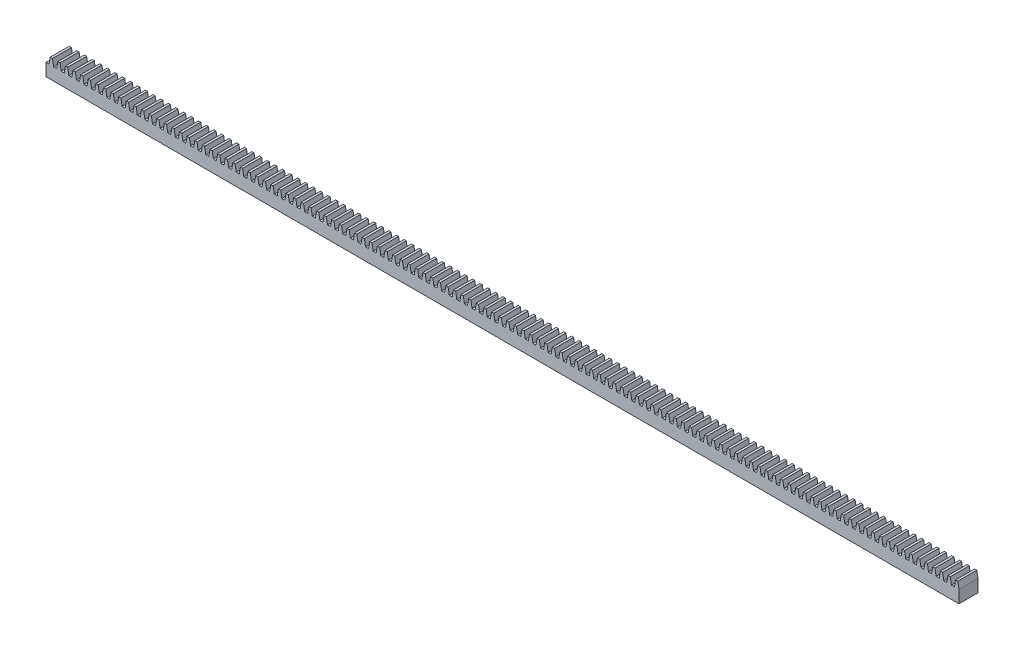
SolidWorks part; units mm, degrees
ref_plane "Front Plane" through (0, 0, 0) normal (0, 0, 1) x (1, 0, 0)
ref_plane "Top Plane" through (0, 0, 0) normal (0, 1, 0) x (1, 0, 0)
ref_plane "Right Plane" through (0, 0, 0) normal (1, 0, 0) x (0, 0, -1)
sketch "Sketch1" plane through (0, 0, 0) normal (1, 0, 0) x (0, 0, -1)
  line L1 (0, 0) -> (6.35, 0)
  line L2 (0, 0) -> (0, 6.35)
  line L3 (0, 6.35) -> (6.35, 6.35)
  line L4 (6.35, 0) -> (6.35, 6.35)
  dimension "D1" = 6.35
  dimension "D2" = 6.35
extrude "Boss-Extrude1" add sketch "Sketch1" against normal blind 304.8
sketch "Sketch2" plane through (0, 0, 0) normal (0, 0, 1) x (1, 0, 0)
  line L0 (0, 6.35) -> (0, 0) construction
  line L1 (-5.08, 4.1402) -> (-5.4696, 6.35)
  line L2 (-4.064, 4.1402) -> (-5.08, 4.1402)
  line L3 (-4.064, 4.1402) -> (-3.6744, 6.35)
  line L4 (-5.4696, 6.35) -> (-3.6744, 6.35)
  line L5 (-1.524, 4.1402) -> (-1.1344, 6.35)
  line L6 (-2.54, 4.1402) -> (-2.9296, 6.35)
  line L7 (-2.9296, 6.35) -> (-1.1344, 6.35)
  line L8 (-7.62, 4.1402) -> (-8.0096, 6.35)
  line L9 (-1.524, 4.1402) -> (-2.54, 4.1402)
  line L10 (-6.604, 4.1402) -> (-7.62, 4.1402)
  line L11 (-6.604, 4.1402) -> (-6.2144, 6.35)
  line L12 (-8.0096, 6.35) -> (-6.2144, 6.35)
  line L13 (-10.16, 4.1402) -> (-10.5496, 6.35)
  line L14 (-9.144, 4.1402) -> (-10.16, 4.1402)
  line L15 (-9.144, 4.1402) -> (-8.7544, 6.35)
  line L16 (-10.5496, 6.35) -> (-8.7544, 6.35)
  line L17 (-12.7, 4.1402) -> (-13.0896, 6.35)
  line L18 (-11.684, 4.1402) -> (-12.7, 4.1402)
  line L19 (-11.684, 4.1402) -> (-11.2944, 6.35)
  line L20 (-13.0896, 6.35) -> (-11.2944, 6.35)
  line L21 (-15.24, 4.1402) -> (-15.6296, 6.35)
  line L22 (-14.224, 4.1402) -> (-15.24, 4.1402)
  line L23 (-14.224, 4.1402) -> (-13.8344, 6.35)
  line L24 (-15.6296, 6.35) -> (-13.8344, 6.35)
  line L25 (-17.78, 4.1402) -> (-18.1696, 6.35)
  line L26 (-16.764, 4.1402) -> (-17.78, 4.1402)
  line L27 (-16.764, 4.1402) -> (-16.3744, 6.35)
  line L28 (-18.1696, 6.35) -> (-16.3744, 6.35)
  line L29 (-20.32, 4.1402) -> (-20.7096, 6.35)
  line L30 (-19.304, 4.1402) -> (-20.32, 4.1402)
  line L31 (-19.304, 4.1402) -> (-18.9144, 6.35)
  line L32 (-20.7096, 6.35) -> (-18.9144, 6.35)
  line L33 (-22.86, 4.1402) -> (-23.2496, 6.35)
  line L34 (-21.844, 4.1402) -> (-22.86, 4.1402)
  line L35 (-21.844, 4.1402) -> (-21.4544, 6.35)
  line L36 (-23.2496, 6.35) -> (-21.4544, 6.35)
  line L37 (-25.4, 4.1402) -> (-25.7896, 6.35)
  line L38 (-24.384, 4.1402) -> (-25.4, 4.1402)
  line L39 (-24.384, 4.1402) -> (-23.9944, 6.35)
  line L40 (-25.7896, 6.35) -> (-23.9944, 6.35)
  line L41 (-27.94, 4.1402) -> (-28.3296, 6.35)
  line L42 (-26.924, 4.1402) -> (-27.94, 4.1402)
  line L43 (-26.924, 4.1402) -> (-26.5344, 6.35)
  line L44 (-28.3296, 6.35) -> (-26.5344, 6.35)
  line L45 (-30.48, 4.1402) -> (-30.8696, 6.35)
  line L46 (-29.464, 4.1402) -> (-30.48, 4.1402)
  line L47 (-29.464, 4.1402) -> (-29.0744, 6.35)
  line L48 (-30.8696, 6.35) -> (-29.0744, 6.35)
  line L49 (-33.02, 4.1402) -> (-33.4096, 6.35)
  line L50 (-32.004, 4.1402) -> (-33.02, 4.1402)
  line L51 (-32.004, 4.1402) -> (-31.6144, 6.35)
  line L52 (-33.4096, 6.35) -> (-31.6144, 6.35)
  line L53 (-35.56, 4.1402) -> (-35.9496, 6.35)
  line L54 (-34.544, 4.1402) -> (-35.56, 4.1402)
  line L55 (-34.544, 4.1402) -> (-34.1544, 6.35)
  line L56 (-35.9496, 6.35) -> (-34.1544, 6.35)
  line L57 (-38.1, 4.1402) -> (-38.4896, 6.35)
  line L58 (-37.084, 4.1402) -> (-38.1, 4.1402)
  line L59 (-37.084, 4.1402) -> (-36.6944, 6.35)
  line L60 (-38.4896, 6.35) -> (-36.6944, 6.35)
  line L61 (-40.64, 4.1402) -> (-41.0296, 6.35)
  line L62 (-39.624, 4.1402) -> (-40.64, 4.1402)
  line L63 (-39.624, 4.1402) -> (-39.2344, 6.35)
  line L64 (-41.0296, 6.35) -> (-39.2344, 6.35)
  line L65 (-43.18, 4.1402) -> (-43.5696, 6.35)
  line L66 (-42.164, 4.1402) -> (-43.18, 4.1402)
  line L67 (-42.164, 4.1402) -> (-41.7744, 6.35)
  line L68 (-43.5696, 6.35) -> (-41.7744, 6.35)
  line L69 (-45.72, 4.1402) -> (-46.1096, 6.35)
  line L70 (-44.704, 4.1402) -> (-45.72, 4.1402)
  line L71 (-44.704, 4.1402) -> (-44.3144, 6.35)
  line L72 (-46.1096, 6.35) -> (-44.3144, 6.35)
  line L73 (-48.26, 4.1402) -> (-48.6496, 6.35)
  line L74 (-47.244, 4.1402) -> (-48.26, 4.1402)
  line L75 (-47.244, 4.1402) -> (-46.8544, 6.35)
  line L76 (-48.6496, 6.35) -> (-46.8544, 6.35)
  line L77 (-50.8, 4.1402) -> (-51.1896, 6.35)
  line L78 (-49.784, 4.1402) -> (-50.8, 4.1402)
  line L79 (-49.784, 4.1402) -> (-49.3944, 6.35)
  line L80 (-51.1896, 6.35) -> (-49.3944, 6.35)
  line L81 (-53.34, 4.1402) -> (-53.7296, 6.35)
  line L82 (-52.324, 4.1402) -> (-53.34, 4.1402)
  line L83 (-52.324, 4.1402) -> (-51.9344, 6.35)
  line L84 (-53.7296, 6.35) -> (-51.9344, 6.35)
  line L85 (-55.88, 4.1402) -> (-56.2696, 6.35)
  line L86 (-54.864, 4.1402) -> (-55.88, 4.1402)
  line L87 (-54.864, 4.1402) -> (-54.4744, 6.35)
  line L88 (-56.2696, 6.35) -> (-54.4744, 6.35)
  line L89 (-58.42, 4.1402) -> (-58.8096, 6.35)
  line L90 (-57.404, 4.1402) -> (-58.42, 4.1402)
  line L91 (-57.404, 4.1402) -> (-57.0144, 6.35)
  line L92 (-58.8096, 6.35) -> (-57.0144, 6.35)
  line L93 (-60.96, 4.1402) -> (-61.3496, 6.35)
  line L94 (-59.944, 4.1402) -> (-60.96, 4.1402)
  line L95 (-59.944, 4.1402) -> (-59.5544, 6.35)
  line L96 (-61.3496, 6.35) -> (-59.5544, 6.35)
  line L97 (-63.5, 4.1402) -> (-63.8896, 6.35)
  line L98 (-62.484, 4.1402) -> (-63.5, 4.1402)
  line L99 (-62.484, 4.1402) -> (-62.0944, 6.35)
  line L100 (-63.8896, 6.35) -> (-62.0944, 6.35)
  line L101 (-66.04, 4.1402) -> (-66.4296, 6.35)
  line L102 (-65.024, 4.1402) -> (-66.04, 4.1402)
  line L103 (-65.024, 4.1402) -> (-64.6344, 6.35)
  line L104 (-66.4296, 6.35) -> (-64.6344, 6.35)
  line L105 (-68.58, 4.1402) -> (-68.9696, 6.35)
  line L106 (-67.564, 4.1402) -> (-68.58, 4.1402)
  line L107 (-67.564, 4.1402) -> (-67.1744, 6.35)
  line L108 (-68.9696, 6.35) -> (-67.1744, 6.35)
  line L109 (-71.12, 4.1402) -> (-71.5096, 6.35)
  line L110 (-70.104, 4.1402) -> (-71.12, 4.1402)
  line L111 (-70.104, 4.1402) -> (-69.7144, 6.35)
  line L112 (-71.5096, 6.35) -> (-69.7144, 6.35)
  line L113 (-73.66, 4.1402) -> (-74.0496, 6.35)
  line L114 (-72.644, 4.1402) -> (-73.66, 4.1402)
  line L115 (-72.644, 4.1402) -> (-72.2544, 6.35)
  line L116 (-74.0496, 6.35) -> (-72.2544, 6.35)
  line L117 (-76.2, 4.1402) -> (-76.5896, 6.35)
  line L118 (-75.184, 4.1402) -> (-76.2, 4.1402)
  line L119 (-75.184, 4.1402) -> (-74.7944, 6.35)
  line L120 (-76.5896, 6.35) -> (-74.7944, 6.35)
  line L121 (-78.74, 4.1402) -> (-79.1296, 6.35)
  line L122 (-77.724, 4.1402) -> (-78.74, 4.1402)
  line L123 (-77.724, 4.1402) -> (-77.3344, 6.35)
  line L124 (-79.1296, 6.35) -> (-77.3344, 6.35)
  line L125 (-81.28, 4.1402) -> (-81.6696, 6.35)
  line L126 (-80.264, 4.1402) -> (-81.28, 4.1402)
  line L127 (-80.264, 4.1402) -> (-79.8744, 6.35)
  line L128 (-81.6696, 6.35) -> (-79.8744, 6.35)
  line L129 (-83.82, 4.1402) -> (-84.2096, 6.35)
  line L130 (-82.804, 4.1402) -> (-83.82, 4.1402)
  line L131 (-82.804, 4.1402) -> (-82.4144, 6.35)
  line L132 (-84.2096, 6.35) -> (-82.4144, 6.35)
  line L133 (-86.36, 4.1402) -> (-86.7496, 6.35)
  line L134 (-85.344, 4.1402) -> (-86.36, 4.1402)
  line L135 (-85.344, 4.1402) -> (-84.9544, 6.35)
  line L136 (-86.7496, 6.35) -> (-84.9544, 6.35)
  line L137 (-88.9, 4.1402) -> (-89.2896, 6.35)
  line L138 (-87.884, 4.1402) -> (-88.9, 4.1402)
  line L139 (-87.884, 4.1402) -> (-87.4944, 6.35)
  line L140 (-89.2896, 6.35) -> (-87.4944, 6.35)
  line L141 (-91.44, 4.1402) -> (-91.8296, 6.35)
  line L142 (-90.424, 4.1402) -> (-91.44, 4.1402)
  line L143 (-90.424, 4.1402) -> (-90.0344, 6.35)
  line L144 (-91.8296, 6.35) -> (-90.0344, 6.35)
  line L145 (-93.98, 4.1402) -> (-94.3696, 6.35)
  line L146 (-92.964, 4.1402) -> (-93.98, 4.1402)
  line L147 (-92.964, 4.1402) -> (-92.5744, 6.35)
  line L148 (-94.3696, 6.35) -> (-92.5744, 6.35)
  line L149 (-96.52, 4.1402) -> (-96.9096, 6.35)
  line L150 (-95.504, 4.1402) -> (-96.52, 4.1402)
  line L151 (-95.504, 4.1402) -> (-95.1144, 6.35)
  line L152 (-96.9096, 6.35) -> (-95.1144, 6.35)
  line L153 (-99.06, 4.1402) -> (-99.4496, 6.35)
  line L154 (-98.044, 4.1402) -> (-99.06, 4.1402)
  line L155 (-98.044, 4.1402) -> (-97.6544, 6.35)
  line L156 (-99.4496, 6.35) -> (-97.6544, 6.35)
  line L157 (-101.6, 4.1402) -> (-101.9896, 6.35)
  line L158 (-100.584, 4.1402) -> (-101.6, 4.1402)
  line L159 (-100.584, 4.1402) -> (-100.1944, 6.35)
  line L160 (-101.9896, 6.35) -> (-100.1944, 6.35)
  line L161 (-104.14, 4.1402) -> (-104.5296, 6.35)
  line L162 (-103.124, 4.1402) -> (-104.14, 4.1402)
  line L163 (-103.124, 4.1402) -> (-102.7344, 6.35)
  line L164 (-104.5296, 6.35) -> (-102.7344, 6.35)
  line L165 (-106.68, 4.1402) -> (-107.0696, 6.35)
  line L166 (-105.664, 4.1402) -> (-106.68, 4.1402)
  line L167 (-105.664, 4.1402) -> (-105.2744, 6.35)
  line L168 (-107.0696, 6.35) -> (-105.2744, 6.35)
  line L169 (-109.22, 4.1402) -> (-109.6096, 6.35)
  line L170 (-108.204, 4.1402) -> (-109.22, 4.1402)
  line L171 (-108.204, 4.1402) -> (-107.8144, 6.35)
  line L172 (-109.6096, 6.35) -> (-107.8144, 6.35)
  line L173 (-111.76, 4.1402) -> (-112.1496, 6.35)
  line L174 (-110.744, 4.1402) -> (-111.76, 4.1402)
  line L175 (-110.744, 4.1402) -> (-110.3544, 6.35)
  line L176 (-112.1496, 6.35) -> (-110.3544, 6.35)
  line L177 (-114.3, 4.1402) -> (-114.6896, 6.35)
  line L178 (-113.284, 4.1402) -> (-114.3, 4.1402)
  line L179 (-113.284, 4.1402) -> (-112.8944, 6.35)
  line L180 (-114.6896, 6.35) -> (-112.8944, 6.35)
  line L181 (-116.84, 4.1402) -> (-117.2296, 6.35)
  line L182 (-115.824, 4.1402) -> (-116.84, 4.1402)
  line L183 (-115.824, 4.1402) -> (-115.4344, 6.35)
  line L184 (-117.2296, 6.35) -> (-115.4344, 6.35)
  line L185 (-119.38, 4.1402) -> (-119.7696, 6.35)
  line L186 (-118.364, 4.1402) -> (-119.38, 4.1402)
  line L187 (-118.364, 4.1402) -> (-117.9744, 6.35)
  line L188 (-119.7696, 6.35) -> (-117.9744, 6.35)
  line L189 (-121.92, 4.1402) -> (-122.3096, 6.35)
  line L190 (-120.904, 4.1402) -> (-121.92, 4.1402)
  line L191 (-120.904, 4.1402) -> (-120.5144, 6.35)
  line L192 (-122.3096, 6.35) -> (-120.5144, 6.35)
  line L193 (-124.46, 4.1402) -> (-124.8496, 6.35)
  line L194 (-123.444, 4.1402) -> (-124.46, 4.1402)
  line L195 (-123.444, 4.1402) -> (-123.0544, 6.35)
  line L196 (-124.8496, 6.35) -> (-123.0544, 6.35)
  line L197 (-127, 4.1402) -> (-127.3896, 6.35)
  line L198 (-125.984, 4.1402) -> (-127, 4.1402)
  line L199 (-125.984, 4.1402) -> (-125.5944, 6.35)
  line L200 (-127.3896, 6.35) -> (-125.5944, 6.35)
  line L201 (-129.54, 4.1402) -> (-129.9296, 6.35)
  line L202 (-128.524, 4.1402) -> (-129.54, 4.1402)
  line L203 (-128.524, 4.1402) -> (-128.1344, 6.35)
  line L204 (-129.9296, 6.35) -> (-128.1344, 6.35)
  line L205 (-132.08, 4.1402) -> (-132.4696, 6.35)
  line L206 (-131.064, 4.1402) -> (-132.08, 4.1402)
  line L207 (-131.064, 4.1402) -> (-130.6744, 6.35)
  line L208 (-132.4696, 6.35) -> (-130.6744, 6.35)
  line L209 (-134.62, 4.1402) -> (-135.0096, 6.35)
  line L210 (-133.604, 4.1402) -> (-134.62, 4.1402)
  line L211 (-133.604, 4.1402) -> (-133.2144, 6.35)
  line L212 (-135.0096, 6.35) -> (-133.2144, 6.35)
  line L213 (-137.16, 4.1402) -> (-137.5496, 6.35)
  line L214 (-136.144, 4.1402) -> (-137.16, 4.1402)
  line L215 (-136.144, 4.1402) -> (-135.7544, 6.35)
  line L216 (-137.5496, 6.35) -> (-135.7544, 6.35)
  line L217 (-139.7, 4.1402) -> (-140.0896, 6.35)
  line L218 (-138.684, 4.1402) -> (-139.7, 4.1402)
  line L219 (-138.684, 4.1402) -> (-138.2944, 6.35)
  line L220 (-140.0896, 6.35) -> (-138.2944, 6.35)
  line L221 (-142.24, 4.1402) -> (-142.6296, 6.35)
  line L222 (-141.224, 4.1402) -> (-142.24, 4.1402)
  line L223 (-141.224, 4.1402) -> (-140.8344, 6.35)
  line L224 (-142.6296, 6.35) -> (-140.8344, 6.35)
  line L225 (-144.78, 4.1402) -> (-145.1696, 6.35)
  line L226 (-143.764, 4.1402) -> (-144.78, 4.1402)
  line L227 (-143.764, 4.1402) -> (-143.3744, 6.35)
  line L228 (-145.1696, 6.35) -> (-143.3744, 6.35)
  line L229 (-147.32, 4.1402) -> (-147.7096, 6.35)
  line L230 (-146.304, 4.1402) -> (-147.32, 4.1402)
  line L231 (-146.304, 4.1402) -> (-145.9144, 6.35)
  line L232 (-147.7096, 6.35) -> (-145.9144, 6.35)
  line L233 (-149.86, 4.1402) -> (-150.2496, 6.35)
  line L234 (-148.844, 4.1402) -> (-149.86, 4.1402)
  line L235 (-148.844, 4.1402) -> (-148.4544, 6.35)
  line L236 (-150.2496, 6.35) -> (-148.4544, 6.35)
  line L237 (-152.4, 4.1402) -> (-152.7896, 6.35)
  line L238 (-151.384, 4.1402) -> (-152.4, 4.1402)
  line L239 (-151.384, 4.1402) -> (-150.9944, 6.35)
  line L240 (-152.7896, 6.35) -> (-150.9944, 6.35)
  line L241 (-154.94, 4.1402) -> (-155.3296, 6.35)
  line L242 (-153.924, 4.1402) -> (-154.94, 4.1402)
  line L243 (-153.924, 4.1402) -> (-153.5344, 6.35)
  line L244 (-155.3296, 6.35) -> (-153.5344, 6.35)
  line L245 (-157.48, 4.1402) -> (-157.8696, 6.35)
  line L246 (-156.464, 4.1402) -> (-157.48, 4.1402)
  line L247 (-156.464, 4.1402) -> (-156.0744, 6.35)
  line L248 (-157.8696, 6.35) -> (-156.0744, 6.35)
  line L249 (-160.02, 4.1402) -> (-160.4096, 6.35)
  line L250 (-159.004, 4.1402) -> (-160.02, 4.1402)
  line L251 (-159.004, 4.1402) -> (-158.6144, 6.35)
  line L252 (-160.4096, 6.35) -> (-158.6144, 6.35)
  line L253 (-162.56, 4.1402) -> (-162.9496, 6.35)
  line L254 (-161.544, 4.1402) -> (-162.56, 4.1402)
  line L255 (-161.544, 4.1402) -> (-161.1544, 6.35)
  line L256 (-162.9496, 6.35) -> (-161.1544, 6.35)
  line L257 (-165.1, 4.1402) -> (-165.4896, 6.35)
  line L258 (-164.084, 4.1402) -> (-165.1, 4.1402)
  line L259 (-164.084, 4.1402) -> (-163.6944, 6.35)
  line L260 (-165.4896, 6.35) -> (-163.6944, 6.35)
  line L261 (-167.64, 4.1402) -> (-168.0296, 6.35)
  line L262 (-166.624, 4.1402) -> (-167.64, 4.1402)
  line L263 (-166.624, 4.1402) -> (-166.2344, 6.35)
  line L264 (-168.0296, 6.35) -> (-166.2344, 6.35)
  line L265 (-170.18, 4.1402) -> (-170.5696, 6.35)
  line L266 (-169.164, 4.1402) -> (-170.18, 4.1402)
  line L267 (-169.164, 4.1402) -> (-168.7744, 6.35)
  line L268 (-170.5696, 6.35) -> (-168.7744, 6.35)
  line L269 (-172.72, 4.1402) -> (-173.1096, 6.35)
  line L270 (-171.704, 4.1402) -> (-172.72, 4.1402)
  line L271 (-171.704, 4.1402) -> (-171.3144, 6.35)
  line L272 (-173.1096, 6.35) -> (-171.3144, 6.35)
  line L273 (-175.26, 4.1402) -> (-175.6496, 6.35)
  line L274 (-174.244, 4.1402) -> (-175.26, 4.1402)
  line L275 (-174.244, 4.1402) -> (-173.8544, 6.35)
  line L276 (-175.6496, 6.35) -> (-173.8544, 6.35)
  line L277 (-177.8, 4.1402) -> (-178.1896, 6.35)
  line L278 (-176.784, 4.1402) -> (-177.8, 4.1402)
  line L279 (-176.784, 4.1402) -> (-176.3944, 6.35)
  line L280 (-178.1896, 6.35) -> (-176.3944, 6.35)
  line L281 (-180.34, 4.1402) -> (-180.7296, 6.35)
  line L282 (-179.324, 4.1402) -> (-180.34, 4.1402)
  line L283 (-179.324, 4.1402) -> (-178.9344, 6.35)
  line L284 (-180.7296, 6.35) -> (-178.9344, 6.35)
  line L285 (-182.88, 4.1402) -> (-183.2696, 6.35)
  line L286 (-181.864, 4.1402) -> (-182.88, 4.1402)
  line L287 (-181.864, 4.1402) -> (-181.4744, 6.35)
  line L288 (-183.2696, 6.35) -> (-181.4744, 6.35)
  line L289 (-185.42, 4.1402) -> (-185.8096, 6.35)
  line L290 (-184.404, 4.1402) -> (-185.42, 4.1402)
  line L291 (-184.404, 4.1402) -> (-184.0144, 6.35)
  line L292 (-185.8096, 6.35) -> (-184.0144, 6.35)
  line L293 (-187.96, 4.1402) -> (-188.3496, 6.35)
  line L294 (-186.944, 4.1402) -> (-187.96, 4.1402)
  line L295 (-186.944, 4.1402) -> (-186.5544, 6.35)
  line L296 (-188.3496, 6.35) -> (-186.5544, 6.35)
  line L297 (-190.5, 4.1402) -> (-190.8896, 6.35)
  line L298 (-189.484, 4.1402) -> (-190.5, 4.1402)
  line L299 (-189.484, 4.1402) -> (-189.0944, 6.35)
  line L300 (-190.8896, 6.35) -> (-189.0944, 6.35)
  line L301 (-193.04, 4.1402) -> (-193.4296, 6.35)
  line L302 (-192.024, 4.1402) -> (-193.04, 4.1402)
  line L303 (-192.024, 4.1402) -> (-191.6344, 6.35)
  line L304 (-193.4296, 6.35) -> (-191.6344, 6.35)
  line L305 (-195.58, 4.1402) -> (-195.9696, 6.35)
  line L306 (-194.564, 4.1402) -> (-195.58, 4.1402)
  line L307 (-194.564, 4.1402) -> (-194.1744, 6.35)
  line L308 (-195.9696, 6.35) -> (-194.1744, 6.35)
  line L309 (-198.12, 4.1402) -> (-198.5096, 6.35)
  line L310 (-197.104, 4.1402) -> (-198.12, 4.1402)
  line L311 (-197.104, 4.1402) -> (-196.7144, 6.35)
  line L312 (-198.5096, 6.35) -> (-196.7144, 6.35)
  line L313 (-200.66, 4.1402) -> (-201.0496, 6.35)
  line L314 (-199.644, 4.1402) -> (-200.66, 4.1402)
  line L315 (-199.644, 4.1402) -> (-199.2544, 6.35)
  line L316 (-201.0496, 6.35) -> (-199.2544, 6.35)
  line L317 (-203.2, 4.1402) -> (-203.5896, 6.35)
  line L318 (-202.184, 4.1402) -> (-203.2, 4.1402)
  line L319 (-202.184, 4.1402) -> (-201.7944, 6.35)
  line L320 (-203.5896, 6.35) -> (-201.7944, 6.35)
  line L321 (-205.74, 4.1402) -> (-206.1296, 6.35)
  line L322 (-204.724, 4.1402) -> (-205.74, 4.1402)
  line L323 (-204.724, 4.1402) -> (-204.3344, 6.35)
  line L324 (-206.1296, 6.35) -> (-204.3344, 6.35)
  line L325 (-208.28, 4.1402) -> (-208.6696, 6.35)
  line L326 (-207.264, 4.1402) -> (-208.28, 4.1402)
  line L327 (-207.264, 4.1402) -> (-206.8744, 6.35)
  line L328 (-208.6696, 6.35) -> (-206.8744, 6.35)
  line L329 (-210.82, 4.1402) -> (-211.2096, 6.35)
  line L330 (-209.804, 4.1402) -> (-210.82, 4.1402)
  line L331 (-209.804, 4.1402) -> (-209.4144, 6.35)
  line L332 (-211.2096, 6.35) -> (-209.4144, 6.35)
  line L333 (-213.36, 4.1402) -> (-213.7496, 6.35)
  line L334 (-212.344, 4.1402) -> (-213.36, 4.1402)
  line L335 (-212.344, 4.1402) -> (-211.9544, 6.35)
  line L336 (-213.7496, 6.35) -> (-211.9544, 6.35)
  line L337 (-215.9, 4.1402) -> (-216.2896, 6.35)
  line L338 (-214.884, 4.1402) -> (-215.9, 4.1402)
  line L339 (-214.884, 4.1402) -> (-214.4944, 6.35)
  line L340 (-216.2896, 6.35) -> (-214.4944, 6.35)
  line L341 (-218.44, 4.1402) -> (-218.8296, 6.35)
  line L342 (-217.424, 4.1402) -> (-218.44, 4.1402)
  line L343 (-217.424, 4.1402) -> (-217.0344, 6.35)
  line L344 (-218.8296, 6.35) -> (-217.0344, 6.35)
  line L345 (-220.98, 4.1402) -> (-221.3696, 6.35)
  line L346 (-219.964, 4.1402) -> (-220.98, 4.1402)
  line L347 (-219.964, 4.1402) -> (-219.5744, 6.35)
  line L348 (-221.3696, 6.35) -> (-219.5744, 6.35)
  line L349 (-223.52, 4.1402) -> (-223.9096, 6.35)
  line L350 (-222.504, 4.1402) -> (-223.52, 4.1402)
  line L351 (-222.504, 4.1402) -> (-222.1144, 6.35)
  line L352 (-223.9096, 6.35) -> (-222.1144, 6.35)
  line L353 (-226.06, 4.1402) -> (-226.4496, 6.35)
  line L354 (-225.044, 4.1402) -> (-226.06, 4.1402)
  line L355 (-225.044, 4.1402) -> (-224.6544, 6.35)
  line L356 (-226.4496, 6.35) -> (-224.6544, 6.35)
  line L357 (-228.6, 4.1402) -> (-228.9896, 6.35)
  line L358 (-227.584, 4.1402) -> (-228.6, 4.1402)
  line L359 (-227.584, 4.1402) -> (-227.1944, 6.35)
  line L360 (-228.9896, 6.35) -> (-227.1944, 6.35)
  line L361 (-231.14, 4.1402) -> (-231.5296, 6.35)
  line L362 (-230.124, 4.1402) -> (-231.14, 4.1402)
  line L363 (-230.124, 4.1402) -> (-229.7344, 6.35)
  line L364 (-231.5296, 6.35) -> (-229.7344, 6.35)
  line L365 (-233.68, 4.1402) -> (-234.0696, 6.35)
  line L366 (-232.664, 4.1402) -> (-233.68, 4.1402)
  line L367 (-232.664, 4.1402) -> (-232.2744, 6.35)
  line L368 (-234.0696, 6.35) -> (-232.2744, 6.35)
  line L369 (-236.22, 4.1402) -> (-236.6096, 6.35)
  line L370 (-235.204, 4.1402) -> (-236.22, 4.1402)
  line L371 (-235.204, 4.1402) -> (-234.8144, 6.35)
  line L372 (-236.6096, 6.35) -> (-234.8144, 6.35)
  line L373 (-238.76, 4.1402) -> (-239.1496, 6.35)
  line L374 (-237.744, 4.1402) -> (-238.76, 4.1402)
  line L375 (-237.744, 4.1402) -> (-237.3544, 6.35)
  line L376 (-239.1496, 6.35) -> (-237.3544, 6.35)
  line L377 (-241.3, 4.1402) -> (-241.6896, 6.35)
  line L378 (-240.284, 4.1402) -> (-241.3, 4.1402)
  line L379 (-240.284, 4.1402) -> (-239.8944, 6.35)
  line L380 (-241.6896, 6.35) -> (-239.8944, 6.35)
  line L381 (-243.84, 4.1402) -> (-244.2296, 6.35)
  line L382 (-242.824, 4.1402) -> (-243.84, 4.1402)
  line L383 (-242.824, 4.1402) -> (-242.4344, 6.35)
  line L384 (-244.2296, 6.35) -> (-242.4344, 6.35)
  line L385 (-246.38, 4.1402) -> (-246.7696, 6.35)
  line L386 (-245.364, 4.1402) -> (-246.38, 4.1402)
  line L387 (-245.364, 4.1402) -> (-244.9744, 6.35)
  line L388 (-246.7696, 6.35) -> (-244.9744, 6.35)
  line L389 (-248.92, 4.1402) -> (-249.3096, 6.35)
  line L390 (-247.904, 4.1402) -> (-248.92, 4.1402)
  line L391 (-247.904, 4.1402) -> (-247.5144, 6.35)
  line L392 (-249.3096, 6.35) -> (-247.5144, 6.35)
  line L393 (-251.46, 4.1402) -> (-251.8496, 6.35)
  line L394 (-250.444, 4.1402) -> (-251.46, 4.1402)
  line L395 (-250.444, 4.1402) -> (-250.0544, 6.35)
  line L396 (-251.8496, 6.35) -> (-250.0544, 6.35)
  line L397 (-254, 4.1402) -> (-254.3896, 6.35)
  line L398 (-252.984, 4.1402) -> (-254, 4.1402)
  line L399 (-252.984, 4.1402) -> (-252.5944, 6.35)
  line L400 (-254.3896, 6.35) -> (-252.5944, 6.35)
  line L401 (-256.54, 4.1402) -> (-256.9296, 6.35)
  line L402 (-255.524, 4.1402) -> (-256.54, 4.1402)
  line L403 (-255.524, 4.1402) -> (-255.1344, 6.35)
  line L404 (-256.9296, 6.35) -> (-255.1344, 6.35)
  line L405 (-259.08, 4.1402) -> (-259.4696, 6.35)
  line L406 (-258.064, 4.1402) -> (-259.08, 4.1402)
  line L407 (-258.064, 4.1402) -> (-257.6744, 6.35)
  line L408 (-259.4696, 6.35) -> (-257.6744, 6.35)
  line L409 (-261.62, 4.1402) -> (-262.0096, 6.35)
  line L410 (-260.604, 4.1402) -> (-261.62, 4.1402)
  line L411 (-260.604, 4.1402) -> (-260.2144, 6.35)
  line L412 (-262.0096, 6.35) -> (-260.2144, 6.35)
  line L413 (-264.16, 4.1402) -> (-264.5496, 6.35)
  line L414 (-263.144, 4.1402) -> (-264.16, 4.1402)
  line L415 (-263.144, 4.1402) -> (-262.7544, 6.35)
  line L416 (-264.5496, 6.35) -> (-262.7544, 6.35)
  line L417 (-266.7, 4.1402) -> (-267.0896, 6.35)
  line L418 (-265.684, 4.1402) -> (-266.7, 4.1402)
  line L419 (-265.684, 4.1402) -> (-265.2944, 6.35)
  line L420 (-267.0896, 6.35) -> (-265.2944, 6.35)
  line L421 (-269.24, 4.1402) -> (-269.6296, 6.35)
  line L422 (-268.224, 4.1402) -> (-269.24, 4.1402)
  line L423 (-268.224, 4.1402) -> (-267.8344, 6.35)
  line L424 (-269.6296, 6.35) -> (-267.8344, 6.35)
  line L425 (-271.78, 4.1402) -> (-272.1696, 6.35)
  line L426 (-270.764, 4.1402) -> (-271.78, 4.1402)
  line L427 (-270.764, 4.1402) -> (-270.3744, 6.35)
  line L428 (-272.1696, 6.35) -> (-270.3744, 6.35)
  line L429 (-274.32, 4.1402) -> (-274.7096, 6.35)
  line L430 (-273.304, 4.1402) -> (-274.32, 4.1402)
  line L431 (-273.304, 4.1402) -> (-272.9144, 6.35)
  line L432 (-274.7096, 6.35) -> (-272.9144, 6.35)
  line L433 (-276.86, 4.1402) -> (-277.2496, 6.35)
  line L434 (-275.844, 4.1402) -> (-276.86, 4.1402)
  line L435 (-275.844, 4.1402) -> (-275.4544, 6.35)
  line L436 (-277.2496, 6.35) -> (-275.4544, 6.35)
  line L437 (-279.4, 4.1402) -> (-279.7896, 6.35)
  line L438 (-278.384, 4.1402) -> (-279.4, 4.1402)
  line L439 (-278.384, 4.1402) -> (-277.9944, 6.35)
  line L440 (-279.7896, 6.35) -> (-277.9944, 6.35)
  line L441 (-281.94, 4.1402) -> (-282.3296, 6.35)
  line L442 (-280.924, 4.1402) -> (-281.94, 4.1402)
  line L443 (-280.924, 4.1402) -> (-280.5344, 6.35)
  line L444 (-282.3296, 6.35) -> (-280.5344, 6.35)
  line L445 (-284.48, 4.1402) -> (-284.8696, 6.35)
  line L446 (-283.464, 4.1402) -> (-284.48, 4.1402)
  line L447 (-283.464, 4.1402) -> (-283.0744, 6.35)
  line L448 (-284.8696, 6.35) -> (-283.0744, 6.35)
  line L449 (-287.02, 4.1402) -> (-287.4096, 6.35)
  line L450 (-286.004, 4.1402) -> (-287.02, 4.1402)
  line L451 (-286.004, 4.1402) -> (-285.6144, 6.35)
  line L452 (-287.4096, 6.35) -> (-285.6144, 6.35)
  line L453 (-289.56, 4.1402) -> (-289.9496, 6.35)
  line L454 (-288.544, 4.1402) -> (-289.56, 4.1402)
  line L455 (-288.544, 4.1402) -> (-288.1544, 6.35)
  line L456 (-289.9496, 6.35) -> (-288.1544, 6.35)
  line L457 (-292.1, 4.1402) -> (-292.4896, 6.35)
  line L458 (-291.084, 4.1402) -> (-292.1, 4.1402)
  line L459 (-291.084, 4.1402) -> (-290.6944, 6.35)
  line L460 (-292.4896, 6.35) -> (-290.6944, 6.35)
  line L461 (-294.64, 4.1402) -> (-295.0296, 6.35)
  line L462 (-293.624, 4.1402) -> (-294.64, 4.1402)
  line L463 (-293.624, 4.1402) -> (-293.2344, 6.35)
  line L464 (-295.0296, 6.35) -> (-293.2344, 6.35)
  line L465 (-297.18, 4.1402) -> (-297.5696, 6.35)
  line L466 (-296.164, 4.1402) -> (-297.18, 4.1402)
  line L467 (-296.164, 4.1402) -> (-295.7744, 6.35)
  line L468 (-297.5696, 6.35) -> (-295.7744, 6.35)
  line L469 (-299.72, 4.1402) -> (-300.1096, 6.35)
  line L470 (-298.704, 4.1402) -> (-299.72, 4.1402)
  line L471 (-298.704, 4.1402) -> (-298.3144, 6.35)
  line L472 (-300.1096, 6.35) -> (-298.3144, 6.35)
  line L473 (-302.26, 4.1402) -> (-302.6496, 6.35)
  line L474 (-301.244, 4.1402) -> (-302.26, 4.1402)
  line L475 (-301.244, 4.1402) -> (-300.8544, 6.35)
  line L476 (-302.6496, 6.35) -> (-300.8544, 6.35)
  line L477 (-304.8, 4.1402) -> (-305.1896, 6.35)
  line L478 (-303.784, 4.1402) -> (-304.8, 4.1402)
  line L479 (-303.784, 4.1402) -> (-303.3944, 6.35)
  line L480 (-305.1896, 6.35) -> (-303.3944, 6.35)
  line L481 (-0.3978, 6.35) -> (0, 6.35)
  line L482 (-0.3978, 6.35) -> (0, 4.1402)
  line L483 (0, 6.35) -> (0, 4.1402)
  dimension "D1" = 1.524
  dimension "D2" = 120
  dimension "D3" = 0.7447
  dimension "D4" = 0.7366
  dimension "D6" = 1.016
extrude "Cut-Extrude1" cut sketch "Sketch2" against normal blind 304.8
sketch "Sketch3" plane through (0, 0, 0) normal (0, -1, 0) x (1, 0, 0)
  line L0 (0, 0) -> (0, -6.35) construction
  circle A0 centre (-19.05, -3.175) radius 1.3462
  circle A1 centre (-152.4, -3.175) radius 1.3462
  circle A2 centre (-285.75, -3.175) radius 1.3462
  dimension "D1" = 2.6924
  dimension "D2" = 2.6924
  dimension "D3" = 2.6924
  dimension "D4" = 19.05
  dimension "D5" = 152.4
  dimension "D6" = 285.75
extrude "Cut-Extrude2" cut sketch "Sketch3" against normal blind 4.572
cosmetic thread "Cosmetic Thread1" parameters "D2"=2.7178
cosmetic thread "Cosmetic Thread2" parameters "D2"=2.7178
cosmetic thread "Cosmetic Thread3" parameters "D2"=2.7178
